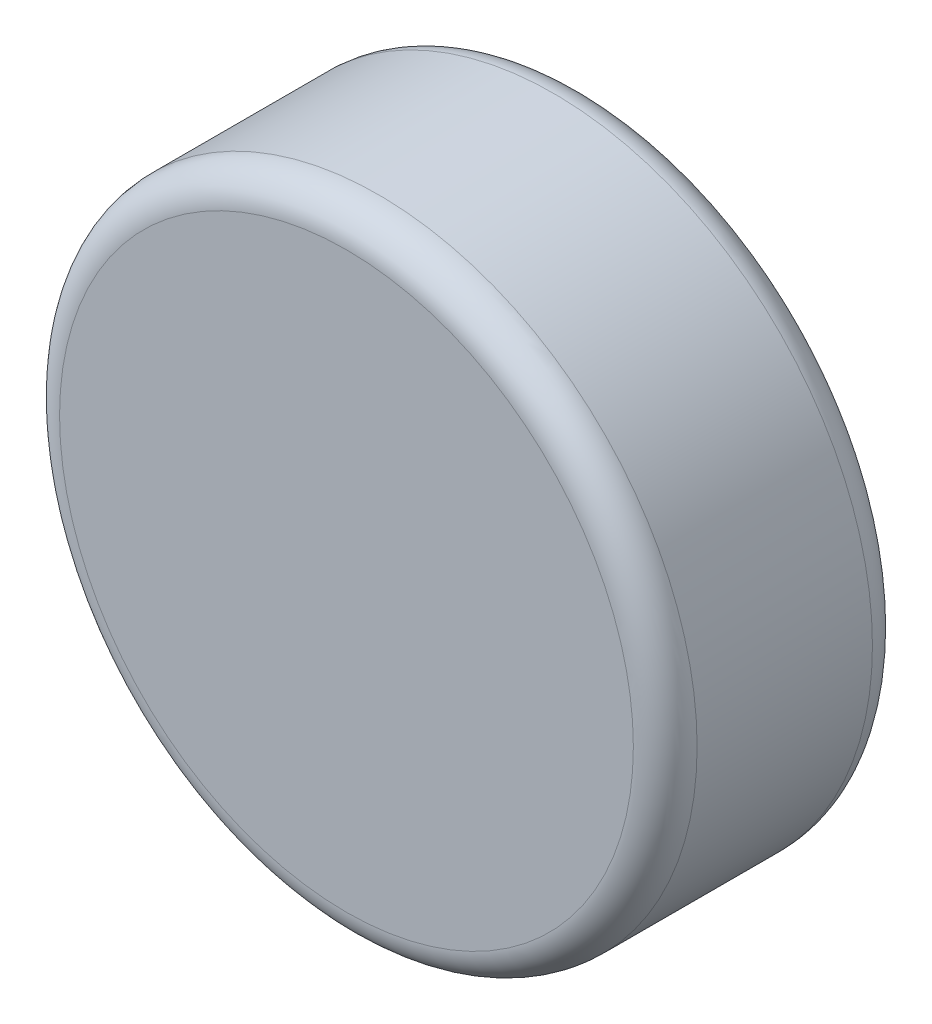
SolidWorks part; units mm, degrees
ref_plane "前视基准面" through (0, 0, 0) normal (0, 0, 1) x (1, 0, 0)
ref_plane "上视基准面" through (0, 0, 0) normal (0, 1, 0) x (1, 0, 0)
ref_plane "右视基准面" through (0, 0, 0) normal (1, 0, 0) x (0, 0, -1)
sketch "草图1" plane through (0, 0, 0) normal (0, 0, 1) x (1, 0, 0)
  circle A0 centre (0, 0) radius 40
  dimension "D1" = 80
extrude "凸台-拉伸1" add sketch "草图1" along normal blind 30
fillet "圆角1" radius 4 2 edges at (40, 0, 30) (40, 0, 0)
